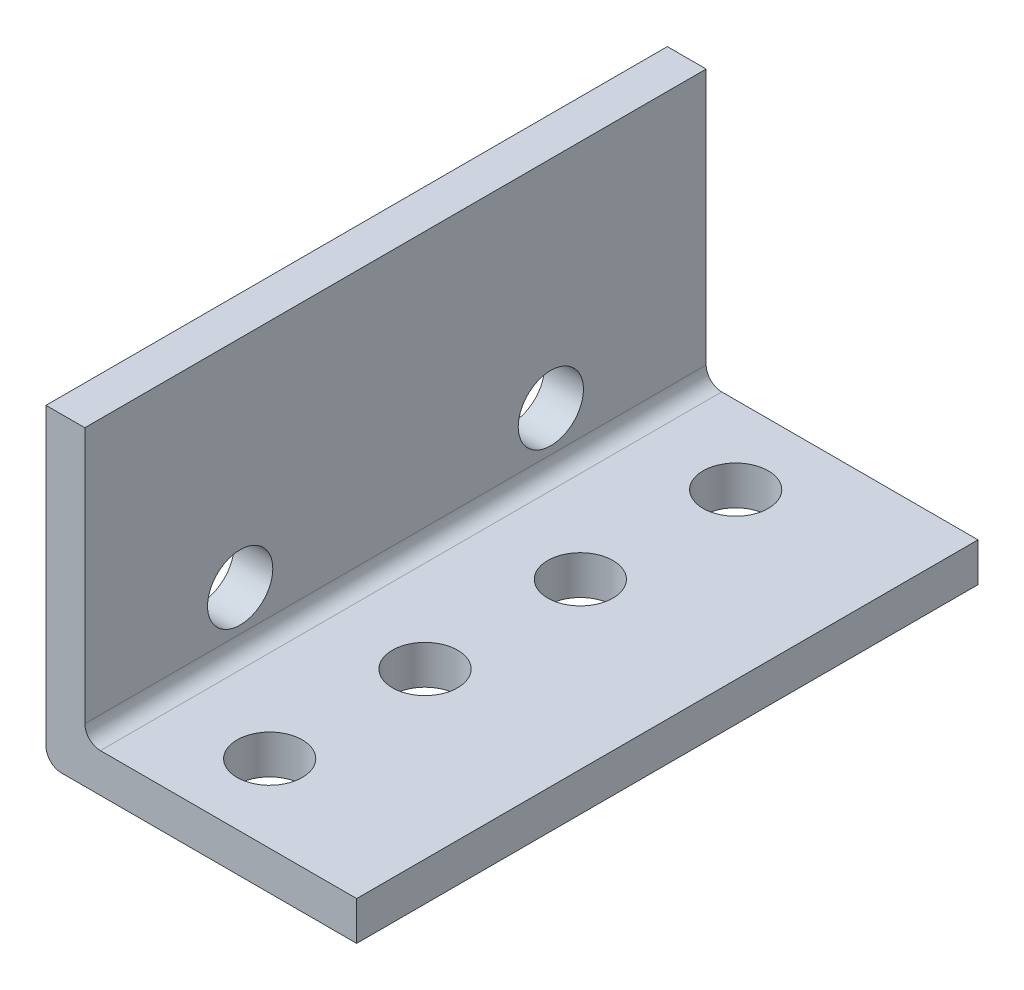
SolidWorks part; units mm, degrees
ref_plane "Front Plane" through (0, 0, 0) normal (0, 0, 1) x (1, 0, 0)
ref_plane "Top Plane" through (0, 0, 0) normal (0, 1, 0) x (1, 0, 0)
ref_plane "Right Plane" through (0, 0, 0) normal (1, 0, 0) x (0, 0, -1)
sketch "Sketch1" plane through (0, 0, 0) normal (0, 0, 1) x (1, 0, 0)
  line L1 (0, -22.225) -> (22.225, -22.225)
  line L2 (22.225, -22.225) -> (22.225, -25.4)
  line L3 (22.225, -25.4) -> (-3.175, -25.4)
  line L4 (-3.175, -25.4) -> (-3.175, 0)
  line L5 (-3.175, 0) -> (0, 0)
  line L6 (0, 0) -> (0, -22.225)
  dimension "D1" = 3.175
  dimension "D2" = 25.4
  dimension "D3" = 22.225
extrude "Boss-Extrude1" add sketch "Sketch1" along normal blind 50.8
sketch "Sketch2" plane through (0, 0, 0) normal (1, 0, 0) x (0, 0, -1)
  line L0 (-25.4, -11.1125) -> (-25.4, 0) construction
  line L1 (-38.1, -11.1125) -> (-38.1, -17.653)
  line L2 (-38.1, -11.1125) -> (-12.7, -11.1125) construction
  line L3 (-50.8, 0) -> (0, 0) construction
  line L4 (-12.7, -11.1125) -> (-12.7, -17.653)
  line L6 (-25.4, -11.1125) -> (-25.4, -22.225) construction
  line L7 (-50.8, -22.225) -> (0, -22.225) construction
  circle A2 centre (-38.1, -17.653) radius 2.667
  circle A3 centre (-12.7, -17.653) radius 2.667
extrude "Cut-Extrude1" cut sketch "Sketch2" against normal through all both and the other way through all
sketch "Sketch3" plane through (0, -22.225, 0) normal (0, 1, 0) x (1, 0, 0)
  line L0 (22.225, -25.4) -> (8.763, -25.4)
  line L1 (22.225, -50.8) -> (22.225, 0) construction
  line L2 (8.763, -19.05) -> (8.763, -31.75)
  line L3 (8.763, -31.75) -> (8.763, -44.45)
  circle A0 centre (8.763, -44.45) radius 2.667
  circle A1 centre (8.763, -31.75) radius 2.667
  circle A2 centre (8.763, -19.05) radius 2.667
  circle A3 centre (8.763, -6.35) radius 2.667
  point P6 (8.763, -25.4)
  dimension "D1" = 4
extrude "Cut-Extrude2" cut sketch "Sketch3" against normal up to surface (3.175 mm away) up to face at (9.525, -25.4, 25.4)
fillet "Fillet1" radius 1.27 1 edges at (0, -22.225, 25.4)
fillet "Fillet2" radius 1.27 1 edges at (-3.175, -25.4, 25.4)
